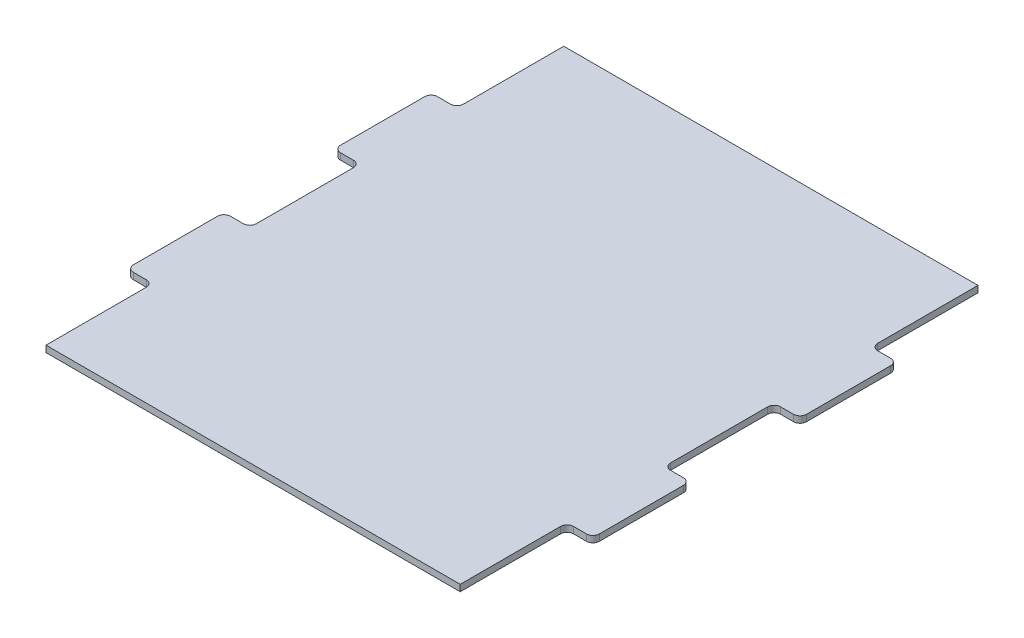
SolidWorks part; units mm, degrees
material "PC High Viscosity"
ref_plane "Front Plane" through (0, 0, 0) normal (0, 0, 1) x (1, 0, 0)
ref_plane "Top Plane" through (0, 0, 0) normal (0, 1, 0) x (1, 0, 0)
ref_plane "Right Plane" through (0, 0, 0) normal (1, 0, 0) x (0, 0, -1)
sketch "Sketch1" plane through (0, 0, 0) normal (0, 1, 0) x (1, 0, 0)
  line L0 (0, 0) -> (0, -254)
  line L1 (0, -254) -> (203.2, -254)
  line L2 (203.2, -254) -> (203.2, 0)
  line L3 (203.2, 0) -> (0, 0)
  dimension "D2" = 203.2
  dimension "D3" = 254
extrude "Boss-Extrude1" add sketch "Sketch1" along normal blind 3.175
sketch "Sketch2" plane through (0, 3.175, 0) normal (0, 1, 0) x (1, 0, 0)
  line L0 (203.2, 0) -> (0, 0) construction
  line L1 (-12.7, -100.0125) -> (215.9, -100.0125)
  line L2 (-12.7, -100.0125) -> (-12.7, -52.3875)
  line L3 (-12.7, -52.3875) -> (215.9, -52.3875)
  line L4 (215.9, -100.0125) -> (215.9, -52.3875)
  line L5 (-12.7, -100.0125) -> (215.9, -52.3875) construction
  line L6 (-12.7, -52.3875) -> (215.9, -100.0125) construction
  line L7 (-12.7, -201.6125) -> (215.9, -201.6125)
  line L8 (-12.7, -201.6125) -> (-12.7, -153.9875)
  line L9 (-12.7, -153.9875) -> (215.9, -153.9875)
  line L10 (215.9, -201.6125) -> (215.9, -153.9875)
  line L11 (-12.7, -201.6125) -> (215.9, -153.9875) construction
  line L12 (-12.7, -153.9875) -> (215.9, -201.6125) construction
  line L13 (0, -254) -> (203.2, -254) construction
  line L14 (0, 0) -> (0, -254) construction
  point P0 (101.6, -76.2)
  point P5 (101.6, -177.8)
  point P13 (101.6, 0)
  dimension "D1" = 76.2
  dimension "D2" = 101.6
  dimension "D3" = 47.625
  dimension "D4" = 12.7
extrude "Boss-Extrude2" add sketch "Sketch2" against normal through all
fillet "Fillet1" radius 3.175 16 edges at (203.2, 1.5875, 201.6125) (215.9, 1.5875, 201.6125) (215.9, 1.5875, 153.9875) (203.2, 1.5875, 153.9875) (203.2, 1.5875, 100.0125) (215.9, 1.5875, 100.0125) (215.9, 1.5875, 52.3875) (203.2, 1.5875, 52.3875) (0, 1.5875, 201.6125) (-12.7, 1.5875, 201.6125) (0, 1.5875, 153.9875) (-12.7, 1.5875, 153.9875) (0, 1.5875, 100.0125) (-12.7, 1.5875, 100.0125) (-12.7, 1.5875, 52.3875) (0, 1.5875, 52.3875)
